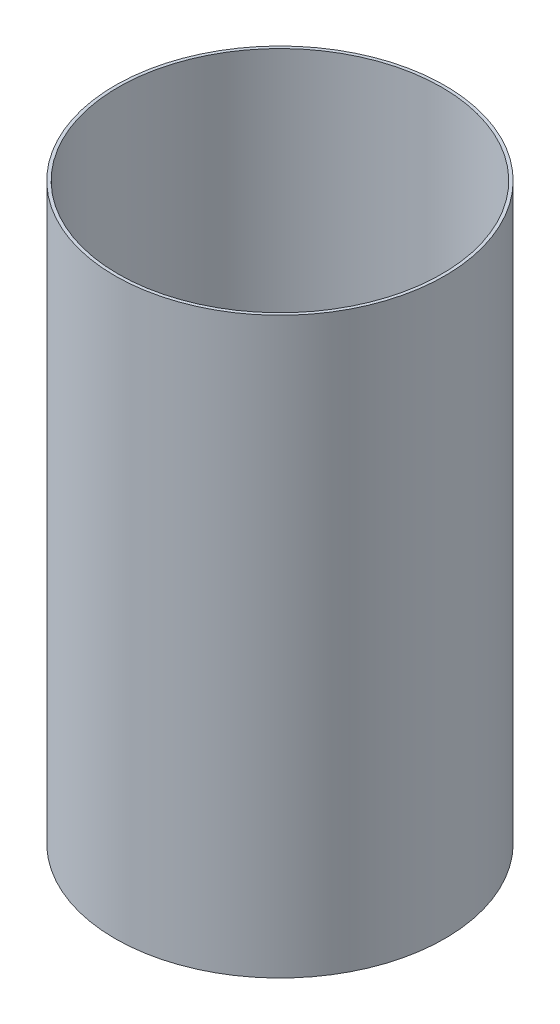
SolidWorks part; units mm, degrees
material "75mm-CastingTube"
ref_plane "Front Plane" through (0, 0, 0) normal (0, 0, 1) x (1, 0, 0)
ref_plane "Top Plane" through (0, 0, 0) normal (0, 1, 0) x (1, 0, 0)
ref_plane "Right Plane" through (0, 0, 0) normal (1, 0, 0) x (0, 0, -1)
sketch "Sketch1" plane through (0, 0, 0) normal (0, 1, 0) x (1, 0, 0)
  circle A0 centre (0, 0) radius 32.4612
  circle A1 centre (0, 0) radius 33.0835
  dimension "D1" = 64.9224
  dimension "D2" = 66.167
extrude "Boss-Extrude1" add sketch "Sketch1" along normal blind 115.1467
